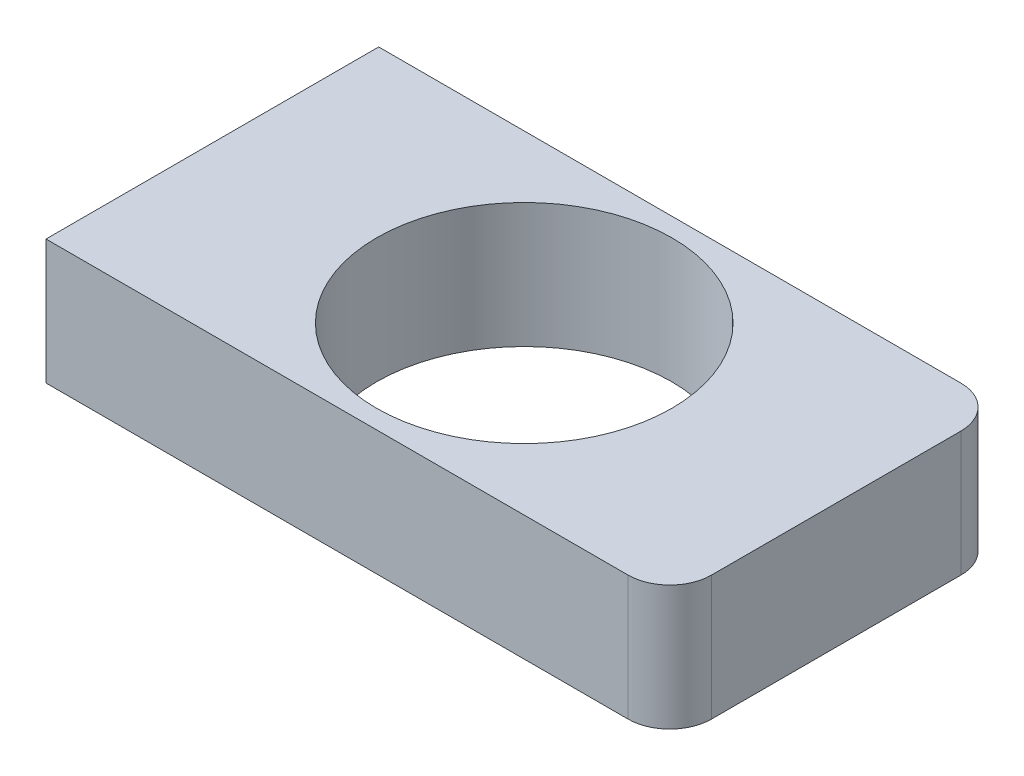
SolidWorks part; units mm, degrees
ref_plane "Front Plane" through (0, 0, 0) normal (0, 0, 1) x (1, 0, 0)
ref_plane "Top Plane" through (0, 0, 0) normal (0, 1, 0) x (1, 0, 0)
ref_plane "Right Plane" through (0, 0, 0) normal (1, 0, 0) x (0, 0, -1)
sketch "Sketch1" plane through (0, 0, 0) normal (0, 1, 0) x (1, 0, 0)
  line L1 (-75, 40) -> (75, 40)
  line L2 (-75, 40) -> (-75, -40)
  line L3 (-75, -40) -> (75, -40)
  line L4 (75, 40) -> (75, -40)
  line L5 (-75, 40) -> (75, -40) construction
  line L6 (-75, -40) -> (75, 40) construction
  point P0 (0, 0)
  dimension "D1" = 150
  dimension "D2" = 80
extrude "Boss-Extrude1" add sketch "Sketch1" along normal mid plane 30
sketch "Sketch2" plane through (0, 15, 0) normal (0, 1, 0) x (1, 0, 0)
  circle A0 centre (0, 0) radius 35.5084
  dimension "D1" = 71.0167
  dimension "D2" = 71.0167
extrude "Cut-Extrude1" cut sketch "Sketch2" against normal through all
fillet "Fillet1" radius 10 2 edges at (75, 0, -40) (75, 0, 40)
fillet "Fillet2" [suppressed] radius 10
